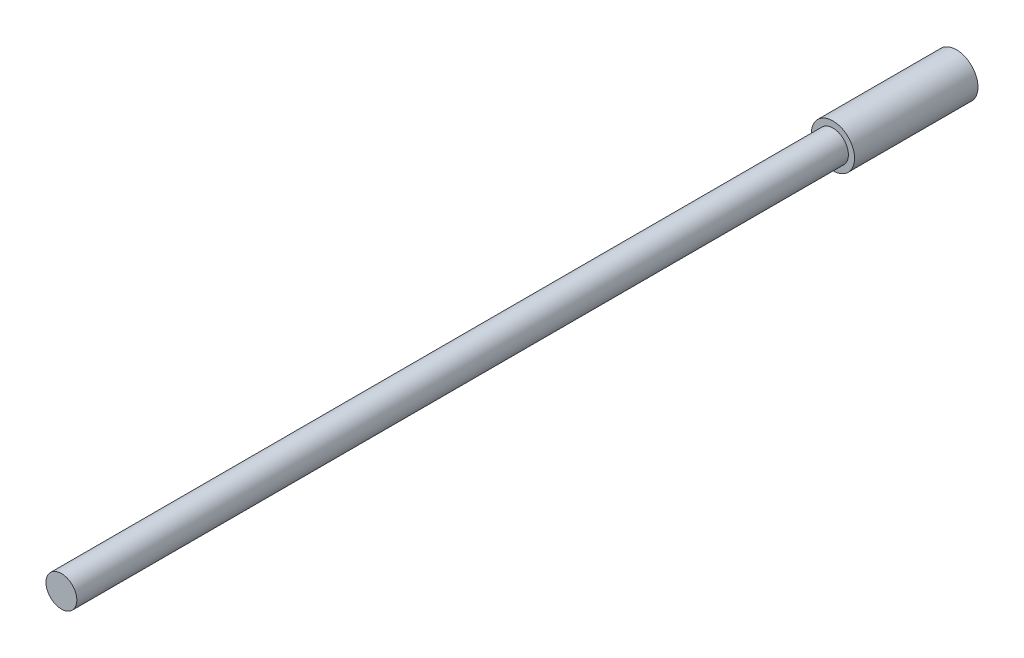
SolidWorks part; units mm, degrees
ref_plane "Front Plane" through (0, 0, 0) normal (0, 0, 1) x (1, 0, 0)
ref_plane "Top Plane" through (0, 0, 0) normal (0, 1, 0) x (1, 0, 0)
ref_plane "Right Plane" through (0, 0, 0) normal (1, 0, 0) x (0, 0, -1)
sketch "Sketch1" plane through (0, 0, 0) normal (0, 0, 1) x (1, 0, 0)
  circle A0 centre (0, 0) radius 0.889
  dimension "D1" = 1.778
extrude "Boss-Extrude1" add sketch "Sketch1" along normal blind 5.08
ref_plane "Plane1" through (0, 0, 5.08) normal (0, 0, 1) x (1, 0, 0)
sketch "Sketch2" plane through (0, 0, 5.08) normal (0, 0, 1) x (1, 0, 0)
  circle A0 centre (0, 0) radius 0.635
  dimension "D1" = 1.27
extrude "Boss-Extrude2" add sketch "Sketch2" along normal blind 31.75
